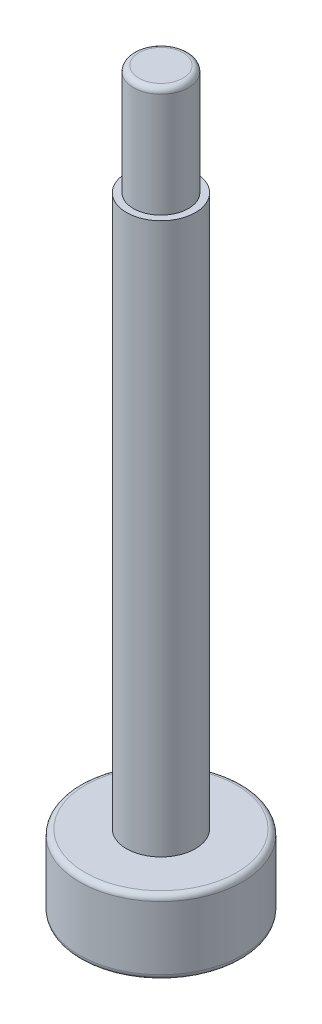
SolidWorks part; units mm, degrees
ref_plane "前视基准面" through (0, 0, 0) normal (0, 0, 1) x (1, 0, 0)
ref_plane "上视基准面" through (0, 0, 0) normal (0, 1, 0) x (1, 0, 0)
ref_plane "右视基准面" through (0, 0, 0) normal (1, 0, 0) x (0, 0, -1)
sketch "草图1" plane through (0, 0, 0) normal (0, 1, 0) x (1, 0, 0)
  circle A0 centre (0, 0) radius 2.95
  dimension "D1" = 5.9
extrude "凸台-拉伸1" add sketch "草图1" along normal blind 2.7
sketch "草图2" plane through (0, 2.7, 0) normal (0, 1, 0) x (1, 0, 0)
  circle A0 centre (0, 0) radius 1.25
  dimension "D1" = 2.5
extrude "凸台-拉伸2" add sketch "草图2" along normal blind 20
sketch "草图3" plane through (0, 22.7, 0) normal (0, 1, 0) x (1, 0, 0)
  circle A0 centre (0, 0) radius 1
  dimension "D1" = 2
extrude "凸台-拉伸3" add sketch "草图3" along normal blind 4
sketch "草图4" plane through (0, 0, 0) normal (0, -1, 0) x (1, 0, 0)
  line L1 (2.2473, -0.532) -> (1.5844, 1.6802)
  line L2 (1.5844, 1.6802) -> (-0.6629, 2.2122)
  line L3 (-0.6629, 2.2122) -> (-2.2473, 0.532)
  line L4 (-2.2473, 0.532) -> (-1.5844, -1.6802)
  line L5 (-1.5844, -1.6802) -> (0.6629, -2.2122)
  line L6 (0.6629, -2.2122) -> (2.2473, -0.532)
  circle A0 centre (0, 0) radius 2 construction
  dimension "D1" = 4
extrude "切除-拉伸1" cut sketch "草图4" against normal blind 2
fillet "圆角1" radius 0.2 3 edges at (0, 0, 2.95) (0, 2.7, 2.95) (0, 26.7, 1)
